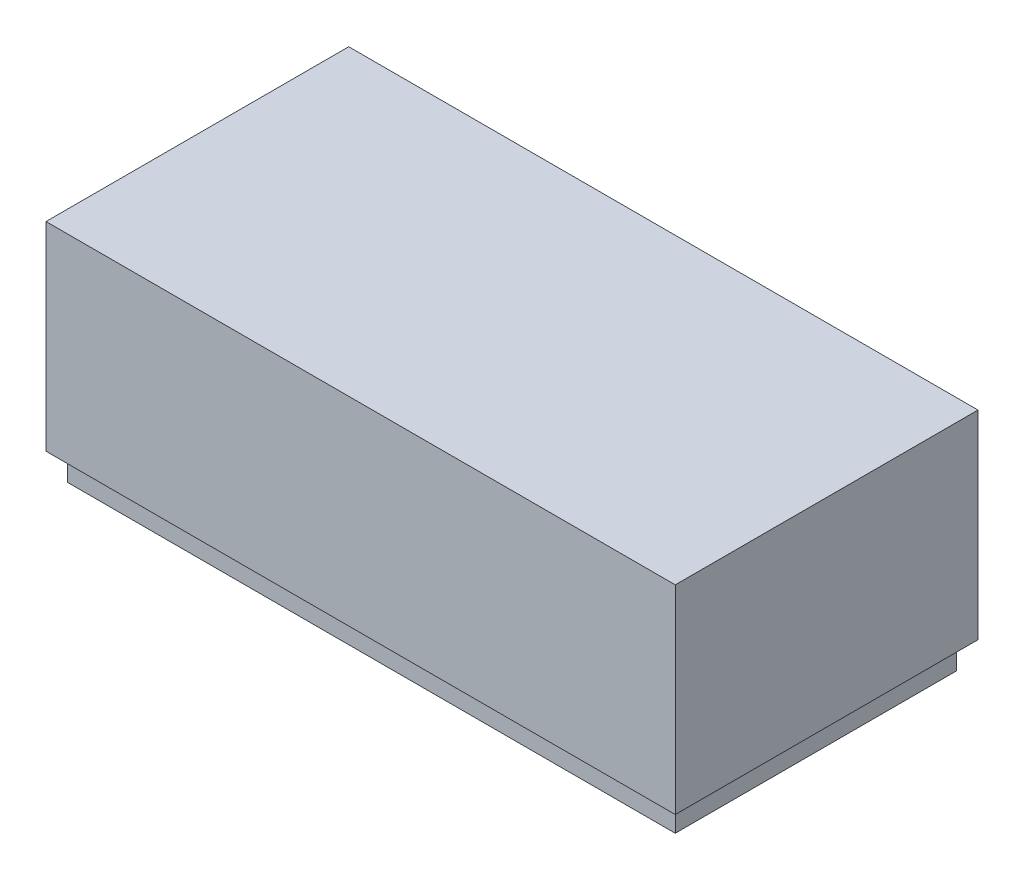
SolidWorks part; units mm, degrees
ref_plane "前视基准面" through (0, 0, 0) normal (0, 0, 1) x (1, 0, 0)
ref_plane "上视基准面" through (0, 0, 0) normal (0, 1, 0) x (1, 0, 0)
ref_plane "右视基准面" through (0, 0, 0) normal (1, 0, 0) x (0, 0, -1)
sketch "草图1" plane through (0, 0, 0) normal (0, 1, 0) x (1, 0, 0)
  line L1 (29.1, -14) -> (-29.1, -14)
  line L2 (29.1, -14) -> (29.1, 14)
  line L3 (29.1, 14) -> (-29.1, 14)
  line L4 (-29.1, -14) -> (-29.1, 14)
  line L5 (29.1, -14) -> (-29.1, 14) construction
  line L6 (29.1, 14) -> (-29.1, -14) construction
  point P0 (0, 0)
  dimension "D1" = 28
  dimension "D2" = 58.2
extrude "凸台-拉伸1" add sketch "草图1" along normal blind 18.4
sketch "草图2" plane through (0, 0, 0) normal (0, -1, 0) x (1, 0, 0)
  line L0 (-28.1, 13) -> (-28.1, -13)
  line L5 (-28.1, -13) -> (28.1, -13)
  line L6 (28.1, -13) -> (28.1, 13)
  line L7 (28.1, 13) -> (-28.1, 13)
  line L8 (-29.1, 14) -> (-29.1, -14)
  line L9 (-29.1, -14) -> (29.1, -14)
  line L10 (29.1, -14) -> (29.1, 14)
  line L11 (29.1, 14) -> (-29.1, 14)
  line L12 (-29.1, 14) -> (-29.1, -14) construction
  line L13 (-29.1, -14) -> (29.1, -14) construction
  line L14 (29.1, -14) -> (29.1, 14) construction
  line L15 (29.1, 14) -> (-29.1, 14) construction
  dimension "D1" = 0
  dimension "D2" = 1
extrude "凸台-拉伸2" add sketch "草图2" along normal blind 2.5
